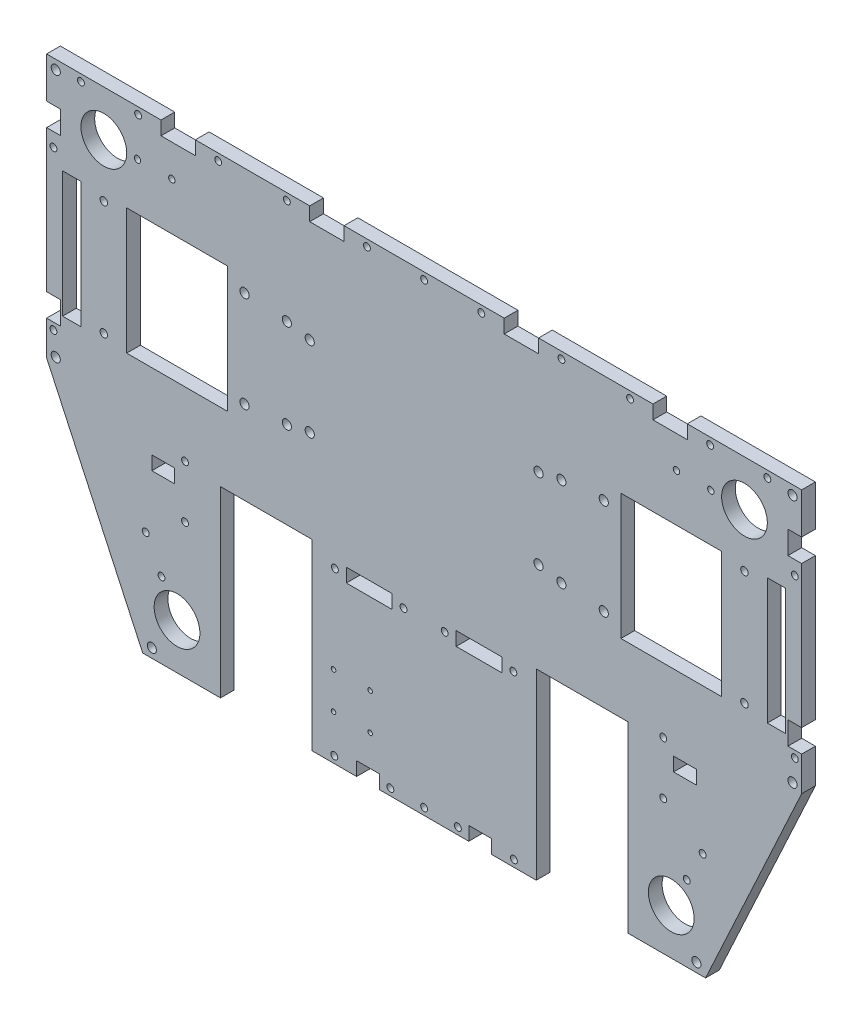
SolidWorks part; units mm, degrees
ref_plane "Plan de face" through (0, 0, 0) normal (0, 0, 1) x (1, 0, 0)
ref_plane "Plan de dessus" through (0, 0, 0) normal (0, 1, 0) x (1, 0, 0)
ref_plane "Plan de droite" through (0, 0, 0) normal (1, 0, 0) x (0, 0, -1)
sketch "Esquisse1" plane through (0, 0, 0) normal (0, 0, 1) x (1, 0, 0)
  line L0 (0, 124.9429) -> (0, -204.46) construction
  line L1 (-165, 96.73) -> (165, 96.73)
  line L2 (165, 96.73) -> (165, -18.27)
  line L3 (165, -18.27) -> (123, -109.0224)
  line L4 (123, -109.0224) -> (-123, -109.0224)
  line L5 (-211.9802, 0) -> (248.5953, 0) construction
  line L6 (-123, -109.0224) -> (-165, -18.27)
  line L7 (-165, -18.27) -> (-165, 96.73)
  circle A0 centre (-23.6, -89.5224) radius 1
  circle A1 centre (-23.6, -73.5224) radius 1
  circle A2 centre (-39.6, -89.5224) radius 1
  circle A3 centre (-39.6, -73.5224) radius 1
  dimension "D15" = 2
  dimension "D16" = 2
  dimension "D17" = 2
  dimension "D18" = 2
  dimension "D24" = 83.4
  dimension "D2" = 165
  dimension "D3" = 330
  dimension "D4" = 100
  dimension "D5" = 115
  dimension "D6" = 100
  dimension "D7" = 246
  dimension "D8" = 205.7524
  dimension "D9" = 96.73
  dimension "D10" = 115
  dimension "D19" = 19.5
  dimension "D20" = 16
  dimension "D21" = 16
  dimension "D22" = 16
  dimension "D23" = 16
extrude "Boss.-Extru.1" add sketch "Esquisse1" along normal blind 6
sketch "Esquisse2" plane through (0, 0, 6) normal (0, 0, 1) x (1, 0, 0)
  line L0 (-123, -109.0224) -> (123, -109.0224) construction
  line L1 (-158, 55.9776) -> (-150, 55.9776)
  line L2 (-158, 55.9776) -> (-158, 0.9776)
  line L3 (-158, 0.9776) -> (-150, 0.9776)
  line L4 (-150, 55.9776) -> (-150, 0.9776)
  line L5 (-130, 55.9776) -> (-86, 55.9776)
  line L6 (-130, 55.9776) -> (-130, 0.9776)
  line L7 (-130, 0.9776) -> (-86, 0.9776)
  line L8 (-86, 55.9776) -> (-86, 0.9776)
  line L9 (0, 145.0258) -> (0, -189.2208) construction
  line L10 (86, 55.9776) -> (86, 0.9776)
  line L11 (130, 0.9776) -> (86, 0.9776)
  line L12 (130, 55.9776) -> (130, 0.9776)
  line L13 (130, 55.9776) -> (86, 55.9776)
  line L14 (150, 55.9776) -> (150, 0.9776)
  line L15 (158, 0.9776) -> (150, 0.9776)
  line L16 (158, 55.9776) -> (158, 0.9776)
  line L17 (158, 55.9776) -> (150, 55.9776)
  line L18 (108, -89.0224) -> (127.6841, -51.1231) construction
  line L19 (89, -109.0224) -> (89, -29.0224)
  line L20 (-49, -109.0224) -> (-89, -109.0224)
  line L21 (-49, -109.0224) -> (-49, -29.0224)
  line L22 (-49, -29.0224) -> (-89, -29.0224)
  line L23 (-89, -109.0224) -> (-89, -29.0224)
  line L24 (49, -29.0224) -> (89, -29.0224)
  line L25 (49, -109.0224) -> (49, -29.0224)
  line L26 (49, -109.0224) -> (89, -109.0224)
  line L27 (-165, 96.73) -> (-165, -18.27) construction
  line L28 (-123, -109.0224) -> (123, -109.0224) construction
  line L29 (165, -18.27) -> (165, 96.73) construction
  line L30 (165, 96.73) -> (-165, 96.73) construction
  circle A0 centre (140, 76.73) radius 10
  circle A1 centre (108, -89.0224) radius 10
  circle A2 centre (-140, 76.73) radius 10
  circle A3 centre (-108, -89.0224) radius 10
  circle A4 centre (161, -16.0224) radius 2
  circle A5 centre (119, -105.0224) radius 2
  circle A6 centre (161, 92.73) radius 2
  circle A7 centre (-161, 92.73) radius 2
  circle A8 centre (-161, -16.0224) radius 2
  circle A9 centre (-119, -105.0224) radius 2
  circle A10 centre (125.27, 76.73) radius 1.4
  circle A11 centre (110.27, 76.73) radius 1.4
  circle A12 centre (114.7893, -75.9504) radius 1.5
  circle A13 centre (121.7031, -62.6388) radius 1.5
  circle A14 centre (-110.27, 76.73) radius 1.4
  circle A15 centre (-125.27, 76.73) radius 1.4
  circle A16 centre (-121.7031, -62.6388) radius 1.5
  circle A17 centre (-114.7893, -75.9504) radius 1.5
  dimension "D16" = 20
  dimension "D17" = 20
  dimension "D18" = 15
  dimension "D19" = 20
  dimension "D20" = 25
  dimension "D21" = 20
  dimension "D24" = 4
  dimension "D15" = 4
  dimension "D25" = 4
  dimension "D28" = 4
  dimension "D29" = 4
  dimension "D30" = 2.8
  dimension "D31" = 2.8
  dimension "D34" = 3
  dimension "D35" = 3
  dimension "D2" = 8
  dimension "D3" = 20
  dimension "D4" = 44
  dimension "D5" = 86
  dimension "D6" = 55
  dimension "D7" = 55
  dimension "D8" = 110
  dimension "D9" = 110
  dimension "D10" = 40
  dimension "D11" = 80
  dimension "D12" = 76
  dimension "D13" = 98
  dimension "D14" = 7
  dimension "D22" = 4
  dimension "D23" = 4
  dimension "D26" = 17
  dimension "D27" = 4
  dimension "D32" = 14.73
  dimension "D33" = 15
  dimension "D36" = 14.73
  dimension "D37" = 15
  dimension "D38" = 37.3159
extrude "Enlèv. mat.-Extru.1" cut sketch "Esquisse2" against normal blind 6
sketch "Esquisse3" plane through (0, 0, 0) normal (0, 0, -1) x (-1, 0, 0)
  line L0 (165, 96.73) -> (165, -18.27) construction
  line L1 (165, -3.27) -> (159, -3.27)
  line L2 (165, -3.27) -> (165, 6.73)
  line L3 (165, 6.73) -> (159, 6.73)
  line L4 (159, -3.27) -> (159, 6.73)
  line L5 (49, -109.0224) -> (-49, -109.0224) construction
  line L6 (165, 68.8526) -> (159, 68.8526)
  line L7 (165, 68.8526) -> (165, 78.8526)
  line L8 (165, 78.8526) -> (159, 78.8526)
  line L9 (159, 68.8526) -> (159, 78.8526)
  line L10 (29.5, -109.0224) -> (19.5, -109.0224)
  line L11 (29.5, -109.0224) -> (29.5, -103.0224)
  line L12 (29.5, -103.0224) -> (19.5, -103.0224)
  line L13 (19.5, -109.0224) -> (19.5, -103.0224)
  line L14 (49, -109.0224) -> (49, -29.0224) construction
  line L15 (0, -209.4812) -> (0, 177.1799) construction
  line L17 (150, 55.9776) -> (158, 55.9776) construction
  line L18 (-19.5, -109.0224) -> (-19.5, -103.0224)
  line L19 (-29.5, -103.0224) -> (-19.5, -103.0224)
  line L20 (-29.5, -109.0224) -> (-29.5, -103.0224)
  line L21 (-29.5, -109.0224) -> (-19.5, -109.0224)
  line L22 (-159, 68.8526) -> (-159, 78.8526)
  line L23 (-165, 78.8526) -> (-159, 78.8526)
  line L24 (-165, 68.8526) -> (-165, 78.8526)
  line L25 (-165, 68.8526) -> (-159, 68.8526)
  line L26 (-159, -3.27) -> (-159, 6.73)
  line L27 (-165, 6.73) -> (-159, 6.73)
  line L28 (-165, -3.27) -> (-165, 6.73)
  line L29 (-165, -3.27) -> (-159, -3.27)
  line L30 (-165, 96.73) -> (165, 96.73) construction
  line L31 (115, 96.73) -> (100, 96.73)
  line L32 (115, 96.73) -> (115, 90.73)
  line L33 (115, 90.73) -> (100, 90.73)
  line L34 (100, 96.73) -> (100, 90.73)
  line L35 (-35, 96.73) -> (-35, 90.73)
  line L36 (50, 96.73) -> (35, 96.73)
  line L37 (50, 96.73) -> (50, 90.73)
  line L38 (50, 90.73) -> (35, 90.73)
  line L39 (35, 96.73) -> (35, 90.73)
  line L40 (-50, 90.73) -> (-35, 90.73)
  line L41 (-50, 96.73) -> (-50, 90.73)
  line L42 (-50, 96.73) -> (-35, 96.73)
  line L43 (-100, 96.73) -> (-100, 90.73)
  line L44 (-115, 90.73) -> (-100, 90.73)
  line L45 (-115, 96.73) -> (-115, 90.73)
  line L46 (-115, 96.73) -> (-100, 96.73)
  dimension "D1" = 10
  dimension "D2" = 6
  dimension "D3" = 6
  dimension "D4" = 10
  dimension "D5" = 10
  dimension "D6" = 6
  dimension "D7" = 19.5
  dimension "D8" = 15
  dimension "D9" = 12.875
  dimension "D10" = 15
  dimension "D11" = 15
  dimension "D12" = 50
  dimension "D13" = 50
  dimension "D14" = 6
extrude "Enlèv. mat.-Extru.2" cut sketch "Esquisse3" against normal blind 6
sketch "Esquisse4" plane through (0, 0, 0) normal (0, 0, -1) x (-1, 0, 0)
  line L0 (159, 68.8526) -> (165, 68.8526) construction
  line L1 (13.1585, 93.73) -> (156.271, 93.73) construction
  line L2 (54.0695, -106.0224) -> (4.75, -106.0224) construction
  line L3 (49, -109.0224) -> (29.5, -109.0224) construction
  line L5 (19.5, -103.0224) -> (19.5, -109.0224) construction
  line L6 (159, -3.27) -> (165, -3.27) construction
  line L7 (29.5, -109.0224) -> (29.5, -103.0224) construction
  line L8 (165, 68.8526) -> (165, 6.73) construction
  line L13 (115, 90.73) -> (115, 96.73) construction
  line L14 (100, 96.73) -> (100, 90.73) construction
  line L15 (50, 90.73) -> (50, 96.73) construction
  line L16 (35, 96.73) -> (35, 90.73) construction
  line L17 (0, 142.2997) -> (0, -202.2086) construction
  circle A0 centre (162, -6.27) radius 1.5
  circle A1 centre (0, -106.0224) radius 1.5
  circle A2 centre (162, 62.8526) radius 1.5
  circle A3 centre (0, 93.73) radius 1.5
  circle A4 centre (-39.25, -106.0224) radius 1.5
  circle A5 centre (-14.75, -106.0224) radius 1.5
  circle A7 centre (14.75, -106.0224) radius 1.5
  circle A9 centre (39.25, -106.0224) radius 1.5
  circle A10 centre (150, 93.73) radius 1.5
  circle A11 centre (125, 93.73) radius 1.5
  circle A12 centre (90, 93.73) radius 1.5
  circle A13 centre (-25, 93.73) radius 1.5
  circle A14 centre (60, 93.73) radius 1.5
  circle A15 centre (25, 93.73) radius 1.5
  circle A16 centre (-60, 93.73) radius 1.5
  circle A17 centre (-90, 93.73) radius 1.5
  circle A18 centre (-125, 93.73) radius 1.5
  circle A19 centre (-150, 93.73) radius 1.5
  circle A31 centre (-162, 62.8526) radius 1.5
  circle A33 centre (-162, -6.27) radius 1.5
  dimension "D3" = 3
  dimension "D10" = 9.75
  dimension "D11" = 3
  dimension "D13" = 3
  dimension "D18" = 3
  dimension "D19" = 3
  dimension "D29" = 3
  dimension "D30" = 3
  dimension "D31" = 3
  dimension "D33" = 3
  dimension "D34" = 3
  dimension "D40" = 10
  dimension "D5" = 3
  dimension "D7" = 3
  dimension "D8" = 3
  dimension "D6" = 6
  dimension "D9" = 3
  dimension "D17" = 4.75
  dimension "D26" = 3
  dimension "D36" = 25
  dimension "D37" = 10
  dimension "D38" = 10
  dimension "D42" = 10
extrude "Enlèv. mat.-Extru.3" cut sketch "Esquisse4" against normal blind 6
sketch "Esquisse5" plane through (0, 0, 0) normal (0, 0, -1) x (-1, 0, 0)
  line L1 (109, -38.0224) -> (119, -38.0224)
  line L2 (109, -38.0224) -> (109, -32.0224)
  line L3 (109, -32.0224) -> (119, -32.0224)
  line L4 (119, -38.0224) -> (119, -32.0224)
  line L5 (0, -159.6455) -> (0, 113.5094) construction
  line L6 (34, -38.0224) -> (14, -38.0224)
  line L7 (34, -38.0224) -> (34, -32.0224)
  line L8 (34, -32.0224) -> (14, -32.0224)
  line L9 (14, -38.0224) -> (14, -32.0224)
  line L10 (49, -109.0224) -> (49, -29.0224) construction
  line L11 (-14, -38.0224) -> (-14, -32.0224)
  line L12 (-34, -32.0224) -> (-14, -32.0224)
  line L13 (-34, -38.0224) -> (-34, -32.0224)
  line L14 (-34, -38.0224) -> (-14, -38.0224)
  line L15 (-119, -38.0224) -> (-119, -32.0224)
  line L16 (-109, -32.0224) -> (-119, -32.0224)
  line L17 (-109, -38.0224) -> (-109, -32.0224)
  line L18 (-109, -38.0224) -> (-119, -38.0224)
  line L19 (89, -29.0224) -> (89, -109.0224) construction
  line L22 (49, -29.0224) -> (89, -29.0224) construction
  dimension "D1" = 10
  dimension "D2" = 20
  dimension "D3" = 15
  dimension "D4" = 6
  dimension "D5" = 6
  dimension "D6" = 3
  dimension "D7" = 3
  dimension "D8" = 20
extrude "Enlèv. mat.-Extru.4" cut sketch "Esquisse5" against normal blind 6
sketch "Esquisse6" plane through (0, 0, 0) normal (0, 0, -1) x (-1, 0, 0)
  line L1 (-165, 6.73) -> (-165, 68.8526) construction
  line L2 (0, 127.7926) -> (0, -140.3318) construction
  line L3 (-42.2546, -35.0224) -> (44.6597, -35.0224) construction
  line L4 (-86, 0.9776) -> (-130, 0.9776) construction
  line L5 (34, -38.0224) -> (34, -32.0224) construction
  line L6 (14, -32.0224) -> (14, -38.0224) construction
  line L7 (-78.5, 7.4776) -> (-78.5, 49.4776) construction
  line L8 (78.5, 7.4776) -> (78.5, 49.4776) construction
  line L10 (113.2167, -35.0224) -> (-121.7916, -35.0224) construction
  line L11 (-130, 55.9776) -> (-86, 55.9776) construction
  line L12 (-50, 45.9776) -> (50, 45.9776) construction
  line L13 (-60, 47.9776) -> (60, 47.9776) construction
  line L14 (-60, 47.9776) -> (-60, 8.9779) construction
  line L15 (-60, 8.9779) -> (60, 8.9779) construction
  line L16 (60, 47.9776) -> (60, 8.9779) construction
  line L18 (-50, 45.9776) -> (-50, 10.9776) construction
  line L19 (-86, 55.9776) -> (-86, 0.9776) construction
  line L20 (-50, 10.9776) -> (50, 10.9776) construction
  line L21 (50, 45.9776) -> (50, 10.9776) construction
  line L22 (-150, 0.9776) -> (-158, 0.9776) construction
  line L24 (104.5, -23.4199) -> (104.5, -49.9442) construction
  line L25 (89, -29.0224) -> (89, -109.0224) construction
  line L26 (49, -29.0224) -> (89, -29.0224) construction
  circle A0 centre (-140, 3.4776) radius 1.65
  circle A1 centre (-140, 53.4776) radius 1.65
  circle A2 centre (140, 53.4776) radius 1.65
  circle A3 centre (140, 3.4776) radius 1.65
  circle A4 centre (-39, -35.0224) radius 1.5
  circle A5 centre (9, -35.0224) radius 1.5
  circle A6 centre (39, -35.0224) radius 1.5
  circle A7 centre (-9, -35.0224) radius 1.5
  circle A8 centre (-78.5, 49.4776) radius 2
  circle A9 centre (-78.5, 7.4776) radius 2
  circle A12 centre (-60, 47.9776) radius 2
  circle A13 centre (-60, 8.9779) radius 2
  circle A14 centre (60, 8.9779) radius 2
  circle A15 centre (60, 47.9776) radius 2
  circle A16 centre (-50, 45.9776) radius 2
  circle A17 centre (50, 45.9776) radius 2
  circle A18 centre (50, 10.9776) radius 2
  circle A19 centre (-50, 10.9776) radius 2
  circle A20 centre (78.5, 7.4776) radius 2
  circle A21 centre (78.5, 49.4776) radius 2
  circle A22 centre (104.5, -27.2224) radius 1.5
  circle A23 centre (104.5, -50.2224) radius 1.5
  circle A24 centre (-104.5, -50.2224) radius 1.5
  circle A25 centre (-104.5, -27.2224) radius 1.5
  point P51 (-86, 28.4776)
  point P70 (89, -69.0224)
  dimension "D1" = 3.3
  dimension "D2" = 3.3
  dimension "D7" = 3
  dimension "D8" = 3
  dimension "D9" = 5
  dimension "D11" = 4
  dimension "D12" = 4
  dimension "D13" = 42
  dimension "D14" = 6.5
  dimension "D16" = 3
  dimension "D17" = 8
  dimension "D18" = 4
  dimension "D19" = 26
  dimension "D20" = 4
  dimension "D21" = 4
  dimension "D22" = 4
  dimension "D29" = 4
  dimension "D30" = 4
  dimension "D31" = 4
  dimension "D32" = 4
  dimension "D34" = 2.5
  dimension "D36" = 1.8
  dimension "D38" = 3
  dimension "D4" = 25
  dimension "D5" = 25
  dimension "D6" = 50
  dimension "D10" = 5
  dimension "D23" = 120
  dimension "D24" = 38.9997
  dimension "D25" = 100
  dimension "D26" = 35
  dimension "D27" = 36
  dimension "D28" = 10
  dimension "D33" = 7.5
  dimension "D35" = 15.5
  dimension "D37" = 23
extrude "Enlèv. mat.-Extru.5" cut sketch "Esquisse6" against normal blind 6
